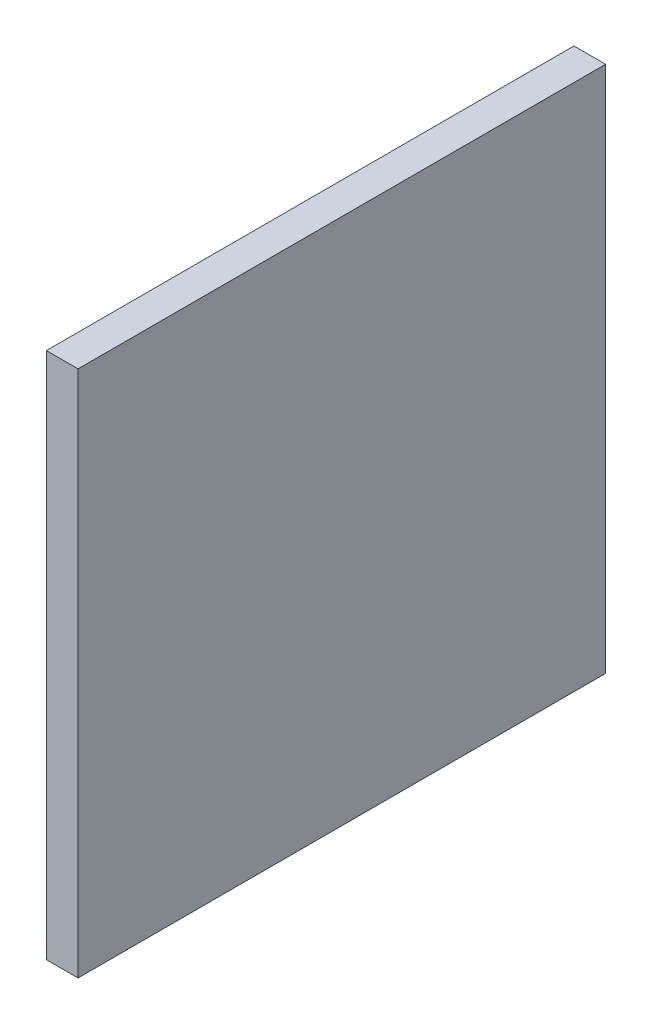
SolidWorks part; units mm, degrees
ref_plane "Plan de face" through (0, 0, 0) normal (0, 0, 1) x (1, 0, 0)
ref_plane "Plan de dessus" through (0, 0, 0) normal (0, 1, 0) x (1, 0, 0)
ref_plane "Plan de droite" through (0, 0, 0) normal (1, 0, 0) x (0, 0, -1)
sketch "Esquisse2" plane through (0, 0, 0) normal (1, 0, 0) x (0, 0, -1)
  line L1 (-79.1818, 13.2738) -> (-29.1818, 13.2738)
  line L2 (-79.1818, 13.2738) -> (-79.1818, -36.7262)
  line L3 (-79.1818, -36.7262) -> (-29.1818, -36.7262)
  line L4 (-29.1818, 13.2738) -> (-29.1818, -36.7262)
  dimension "D1" = 50
  dimension "D2" = 50
extrude "Boss.-Extru.1" add sketch "Esquisse2" along normal blind 3
